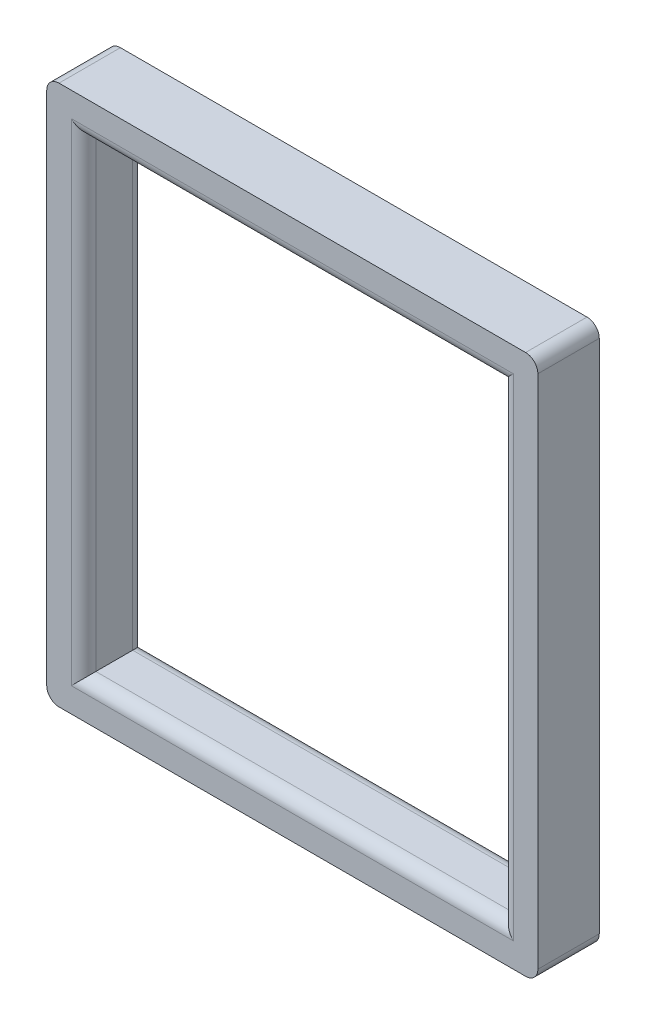
SolidWorks part; units mm, degrees
material "C110 COPPER"
ref_plane "Front Plane" through (0, 0, 0) normal (0, 0, 1) x (1, 0, 0)
ref_plane "Top Plane" through (0, 0, 0) normal (0, 1, 0) x (1, 0, 0)
ref_plane "Right Plane" through (0, 0, 0) normal (1, 0, 0) x (0, 0, -1)
sketch "Sketch1" plane through (0, 0, 0) normal (0, 0, 1) x (1, 0, 0)
  line L1 (-10.795, -12.065) -> (10.795, -12.065)
  line L2 (-10.795, -12.065) -> (-10.795, 12.065)
  line L3 (-10.795, 12.065) -> (10.795, 12.065)
  line L4 (10.795, -12.065) -> (10.795, 12.065)
  line L5 (-10.795, -12.065) -> (10.795, 12.065) construction
  line L6 (-10.795, 12.065) -> (10.795, -12.065) construction
  line L7 (-12.7, -13.97) -> (12.7, -13.97)
  line L8 (-12.7, -13.97) -> (-12.7, 13.97)
  line L9 (-12.7, 13.97) -> (12.7, 13.97)
  line L10 (12.7, -13.97) -> (12.7, 13.97)
  line L11 (-12.7, -13.97) -> (12.7, 13.97) construction
  line L12 (-12.7, 13.97) -> (12.7, -13.97) construction
  point P0 (0, 0)
  point P5 (0, 0)
  dimension "D1" = 21.59
  dimension "D2" = 25.4
  dimension "D3" = 24.13
  dimension "D4" = 27.94
extrude "Boss-Extrude1" add sketch "Sketch1" along normal blind 3.175
fillet "Fillet1" radius 0.635 12 edges at (0, 12.065, 3.175) (0, 12.065, 0) (10.795, 0, 0) (10.795, 0, 3.175) (0, -12.065, 3.175) (0, -12.065, 0) (-10.795, 0, 0) (-10.795, 0, 3.175) (-12.7, -13.97, 1.5875) (12.7, -13.97, 1.5875) (12.7, 13.97, 1.5875) (-12.7, 13.97, 1.5875)
